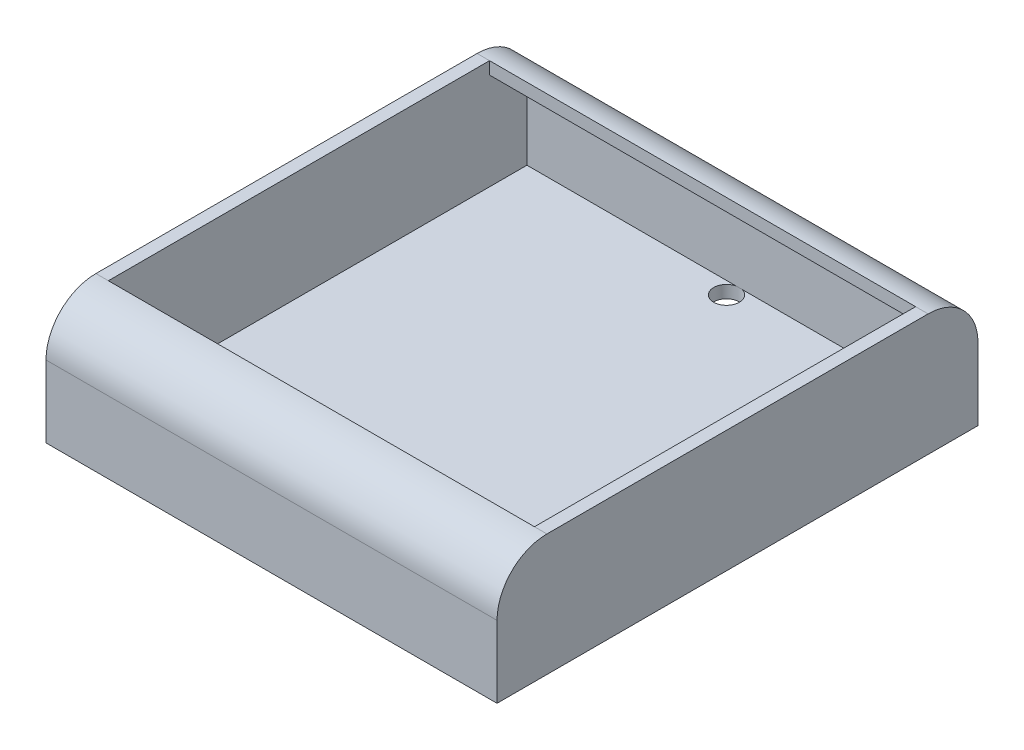
SolidWorks part; units mm, degrees
material "ABS"
ref_plane "Front Plane" through (0, 0, 0) normal (0, 0, 1) x (1, 0, 0)
ref_plane "Top Plane" through (0, 0, 0) normal (0, 1, 0) x (1, 0, 0)
ref_plane "Right Plane" through (0, 0, 0) normal (1, 0, 0) x (0, 0, -1)
sketch "Sketch1" plane through (0, 0, 0) normal (0, 1, 0) x (1, 0, 0)
  line L1 (0, 0) -> (57.404, 0)
  line L2 (0, 0) -> (0, -61.214)
  line L3 (0, -61.214) -> (57.404, -61.214)
  line L4 (57.404, 0) -> (57.404, -61.214)
  dimension "D1" = 57.404
  dimension "D2" = 61.214
extrude "Boss-Extrude1" add sketch "Sketch1" along normal blind 1.5875
sketch "Sketch2" plane through (57.404, 0, 0) normal (1, 0, 0) x (0, 0, -1)
  line L0 (0, 1.5875) -> (0, 0) construction
  line L1 (-61.214, 1.5875) -> (0, 1.5875)
  line L2 (-61.214, 1.5875) -> (-61.214, 9.144)
  line L3 (-54.864, 15.494) -> (-6.35, 15.494)
  line L4 (0, 1.5875) -> (0, 9.144)
  line L5 (-61.214, 0) -> (0, 0) construction
  arc A0 (-6.35, 15.494) -> (0, 9.144) centre (-6.35, 9.144) cw
  arc A1 (-54.864, 15.494) -> (-61.214, 9.144) centre (-54.864, 9.144) ccw
  point P7 (0, 0.7937)
  dimension "D1" = 6.35
  dimension "D2" = 15.494
extrude "Boss-Extrude2" add sketch "Sketch2" against normal blind 1.5875
sketch "Sketch3" plane through (55.8165, 0, 0) normal (-1, 0, 0) x (0, 0, 1)
  line L4 (1.5875, 3.175) -> (1.5875, 1.5875)
  line L5 (61.214, 1.5875) -> (0, 1.5875) construction
  line L6 (59.6265, 3.175) -> (59.6265, 1.5875)
  line L7 (6.35, 13.9065) -> (6.35, 15.494)
  line L8 (59.6265, 3.175) -> (59.6265, 9.144)
  line L9 (54.864, 13.9065) -> (6.35, 13.9065)
  line L10 (1.5875, 9.144) -> (1.5875, 3.175)
  line L11 (1.5875, 3.175) -> (59.6265, 3.175)
  line L12 (59.6265, 3.175) -> (59.6265, 9.144)
  line L13 (54.864, 13.9065) -> (6.35, 13.9065)
  line L14 (1.5875, 9.144) -> (1.5875, 3.175)
  line L15 (1.5875, 3.175) -> (59.6265, 3.175)
  line L16 (54.864, 13.9065) -> (54.864, 15.494)
  arc A2 (6.35, 15.494) -> (0, 9.144) centre (6.35, 9.144) ccw construction
  arc A4 (59.6265, 9.144) -> (54.864, 13.9065) centre (54.864, 9.144) ccw
  arc A5 (6.35, 13.9065) -> (1.5875, 9.144) centre (6.35, 9.144) ccw
  arc A6 (59.6265, 9.144) -> (54.864, 13.9065) centre (54.864, 9.144) ccw
  arc A7 (6.35, 13.9065) -> (1.5875, 9.144) centre (6.35, 9.144) ccw
  line M7 (61.214, 1.5875) -> (61.214, 9.144)
  arc M8 (61.214, 9.144) -> (54.864, 15.494) centre (54.864, 9.144) ccw
  arc M10 (6.35, 15.494) -> (0, 9.144) centre (6.35, 9.144) ccw
  line M11 (0, 9.144) -> (0, 1.5875)
  line M12 (0, 1.5875) -> (61.214, 1.5875)
  dimension "D1" = 1.5875
extrude "Boss-Extrude3" add sketch "Sketch3" along normal offset from surface (54.229 mm away) 1.5875 contours A7 L7 L4 L14 M10 M11 M12 | A6 L12 L6 L16 M12 M7 M8 up to face at (0, 0.7937, 30.607)
sketch "Sketch4" plane through (1.5875, 0, 0) normal (-1, 0, 0) x (0, 0, 1)
  line L4 (0, 0) -> (61.214, 0)
  line L5 (0, 9.144) -> (0, 0)
  line L6 (54.864, 15.494) -> (6.35, 15.494)
  line L7 (61.214, 0) -> (61.214, 9.144)
  line L8 (0, 0) -> (61.214, 0)
  line L9 (0, 9.144) -> (0, 0)
  line L10 (54.864, 15.494) -> (6.35, 15.494)
  line L11 (61.214, 0) -> (61.214, 9.144)
  arc A2 (6.35, 15.494) -> (0, 9.144) centre (6.35, 9.144) ccw
  arc A3 (61.214, 9.144) -> (54.864, 15.494) centre (54.864, 9.144) ccw
  arc A4 (6.35, 15.494) -> (0, 9.144) centre (6.35, 9.144) ccw
  arc A5 (61.214, 9.144) -> (54.864, 15.494) centre (54.864, 9.144) ccw
  dimension "D1" = 0
extrude "Boss-Extrude4" add sketch "Sketch4" along normal blind 1.5875
hole_wizard "#4 Clearance Hole1" positions "Sketch5" profile "Sketch6" hole size "#4" standard "ANSI Inch"
sketch "Sketch5" plane through (0, 1.5875, 0) normal (0, 1, 0) x (1, 0, 0)
  line L0 (28.575, -58.039) -> (28.575, -3.175)
  line L10 (57.404, 0) -> (0, 0)
  line L11 (57.404, -61.214) -> (57.404, 0)
  line L12 (0, -61.214) -> (57.404, -61.214)
  line L14 (57.404, 0) -> (0, 0)
  line L15 (57.404, -61.214) -> (57.404, 0)
  line L16 (0, -61.214) -> (57.404, -61.214)
  line L17 (28.575, -3.175) -> (28.575, 0)
  line L19 (28.575, -58.039) -> (28.575, -61.214)
  line L43 (0, 0) -> (0, -61.214)
  line L44 (0, 0) -> (0, -61.214)
  point P0 (28.575, -58.039)
  point P2 (28.575, -3.175)
  dimension "D1" = 54.864
  dimension "D3" = 28.575
  dimension "D2" = 0
sketch "Sketch6" plane through (28.575, 1.5875, 58.039) normal (1, 0, 0) x (0, 0, 1)
  line L0 (0, 0) -> (0, 1.5875)
  line L1 (0, 1.5875) -> (1.6319, 1.5875)
  line L2 (1.6319, 1.5875) -> (1.6319, 0)
  line L5 (1.6319, 0) -> (0, 0)
  line L11 (0, -6.35) -> (0, 107.95) construction
  dimension "Thru Hole Dia." = 3.2639
  dimension "Thru Hole Depth" = 1.5875
sketch "Sketch8" plane through (57.404, 0, 0) normal (1, 0, 0) x (0, 0, -1)
  text T0 "FRONT"
